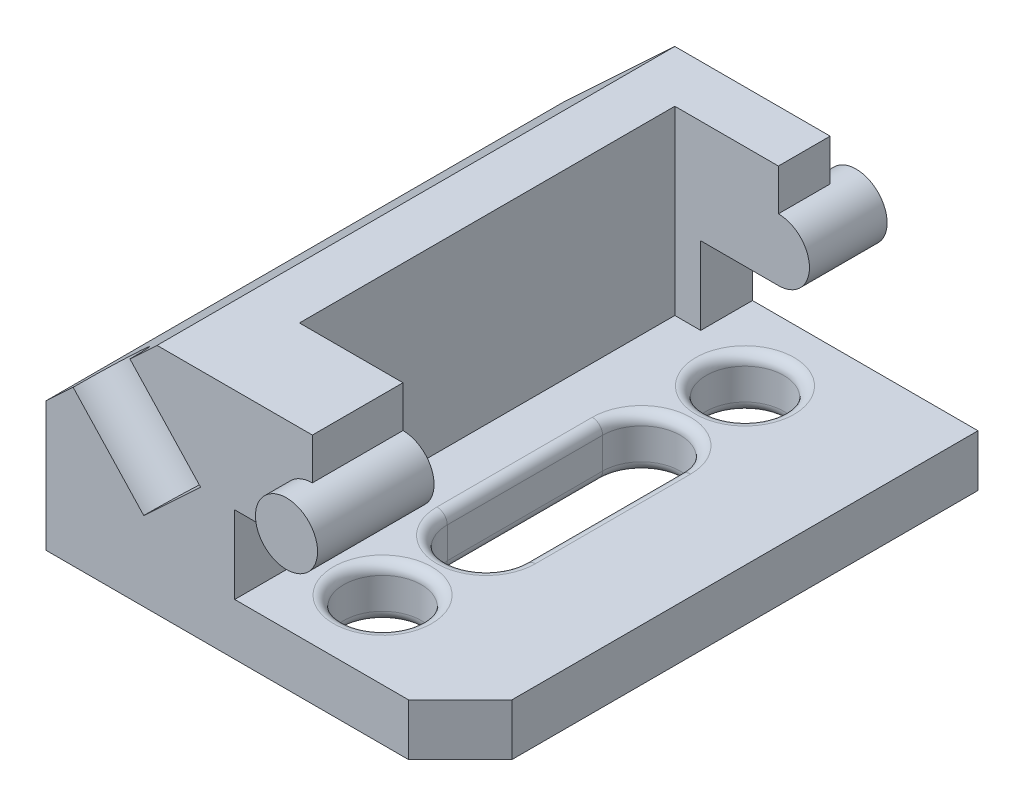
SolidWorks part; units mm, degrees
material "Stop 1060"
ref_plane "Płaszczyzna przednia" through (0, 0, 0) normal (0, 0, 1) x (1, 0, 0)
ref_plane "Płaszczyzna górna" through (0, 0, 0) normal (0, 1, 0) x (1, 0, 0)
ref_plane "Płaszczyzna prawa" through (0, 0, 0) normal (1, 0, 0) x (0, 0, -1)
sketch "Szkic2" plane through (0, 0, 0) normal (0, 0, 1) x (1, 0, 0)
  line L0 (0, 0) -> (80, 0)
  line L1 (80, 0) -> (80, 10)
  line L2 (80, 10) -> (36.4474, 10)
  line L3 (36.4474, 10) -> (36.4474, 25)
  line L4 (36.4474, 25) -> (51.4474, 25)
  line L5 (51.4474, 37) -> (51.4474, 45)
  line L6 (51.4474, 45) -> (21.4474, 45)
  line L7 (21.4474, 45) -> (0, 25)
  line L8 (0, 25) -> (0, 0)
  arc A0 (51.4474, 25) -> (51.4474, 37) centre (51.4474, 31) ccw
  point P9 (57.4474, 31)
  dimension "D3" = 15
  dimension "D1" = 30
  dimension "D2" = 6
  dimension "D4" = 47
  dimension "D5" = 20
  dimension "D6" = 25
  dimension "D7" = 80
  dimension "D8" = 15
  dimension "D9" = 10
extrude "Dodanie-wyciągnięcie1" add sketch "Szkic2" along normal blind 100
chamfer "Sfazowanie1" distance 10 angle 45 1 edges at (80, 5, 100)
sketch "Szkic3" plane through (0, 0, 100) normal (0, 0, 1) x (1, 0, 0)
  circle A0 centre (51.4474, 31) radius 6
  arc A1 (51.4474, 25) -> (51.4474, 37) centre (51.4474, 31) ccw construction
  point P2 (0, 0)
extrude "Dodanie-wyciągnięcie2" add sketch "Szkic3" along normal blind 5 and the other way blind 105 contours A0
sketch "Szkic4" plane through (0, 45, 0) normal (0, 1, 0) x (1, 0, 0)
  line L0 (21.4474, -100) -> (21.4474, 0) construction
  line L1 (31.4474, -10) -> (57.4474, -10)
  line L2 (31.4474, -10) -> (31.4474, -82.5)
  line L3 (31.4474, -82.5) -> (57.4474, -82.5)
  line L4 (57.4474, -10) -> (57.4474, -82.5)
  line L5 (57.4474, -105) -> (57.4474, 5) construction
  line L6 (51.4474, 0) -> (21.4474, 0) construction
  dimension "D1" = 10
  dimension "D2" = 72.5
  dimension "D3" = 10
extrude "Wytnij-wyciągnięcie1" cut sketch "Szkic4" against normal up to surface (35 mm away) up to face at (60.5789, 10, 58)
sketch "Szkic5" plane through (0, 10, 0) normal (0, 1, 0) x (1, 0, 0)
  line L1 (70, -100) -> (36.4474, -100) construction
  line L2 (80, -90) -> (80, 0) construction
  line L3 (42.5, -35) -> (42.5, -65)
  line L4 (57.5, -35) -> (57.5, -65)
  circle A0 centre (50, -15) radius 7.5
  arc A1 (57.5, -35) -> (42.5, -35) centre (50, -35) ccw
  arc A2 (42.5, -65) -> (57.5, -65) centre (50, -65) ccw
  circle A3 centre (50, -85) radius 7.5
  dimension "D1" = 15
  dimension "D2" = 15
  dimension "D3" = 15
  dimension "D4" = 15
  dimension "D5" = 15
  dimension "D6" = 20
  dimension "D7" = 20
  dimension "D8" = 15
  dimension "D9" = 30
  dimension "D10" = 30
extrude "Wytnij-wyciągnięcie3" cut sketch "Szkic5" against normal through all
fillet "Zaokrąglenie2" radius 2 12 edges at (50, 0, 27.5) (50, 10, 27.5) (57.5, 0, 50) (57.5, 10, 50) (50, 0, 72.5) (50, 10, 72.5) (42.5, 0, 50) (42.5, 10, 50) (42.5, 10, 85) (42.5, 0, 85) (42.5, 10, 15) (42.5, 0, 15)
sketch "Szkic6" plane through (-12.4696, 13.372, 0) normal (-0.682, 0.7314, 0) x (0.7314, 0.682, 0)
  line L0 (46.3755, -100) -> (17.05, -100) construction
  circle A0 centre (31.7128, -100) radius 7.5
  point P2 (0, 0)
  point P6 (31.7128, -100)
  dimension "D1" = 15
extrude "Wytnij-wyciągnięcie5" cut sketch "Szkic6" against normal blind 20
